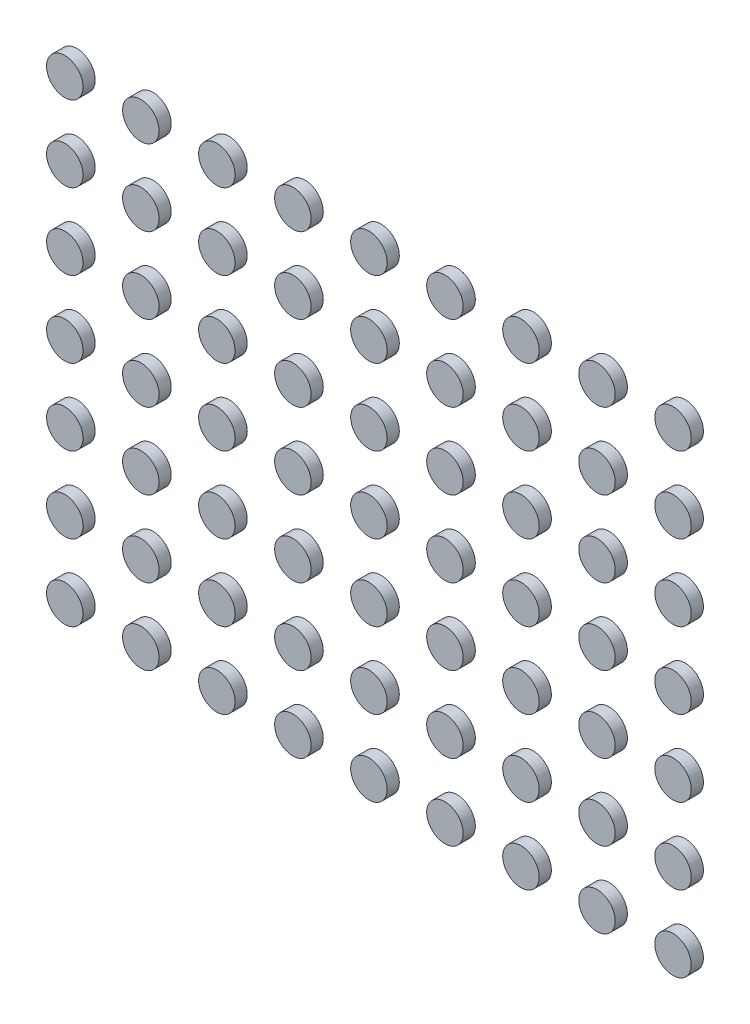
SolidWorks part; units mm, degrees
ref_plane "前视基准面" through (0, 0, 0) normal (0, 0, 1) x (1, 0, 0)
ref_plane "上视基准面" through (0, 0, 0) normal (0, 1, 0) x (1, 0, 0)
ref_plane "右视基准面" through (0, 0, 0) normal (1, 0, 0) x (0, 0, -1)
other "Configuration Table"
sketch "草图1" plane through (0, 0, 0) normal (0, 0, 1) x (1, 0, 0)
  circle A0 centre (0, 0) radius 0.6
  dimension "D1" = 1.2
extrude "凸台-拉伸1" add sketch "草图1" along normal blind 0.4
pattern_linear "阵列(线性)1" count 9 spacing 2.5 along (1, 0, 0) count 7 spacing 2.5 along (0, 1, 0) of "凸台-拉伸1"
